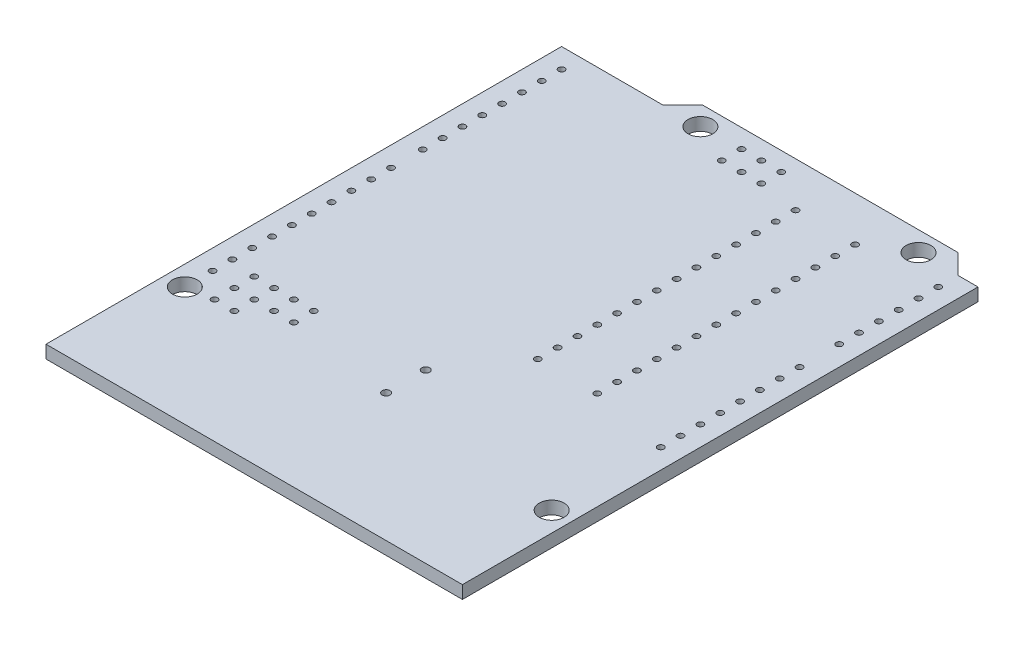
SolidWorks part; units mm, degrees
material "E-Glass Fiber"
ref_plane "Front Plane" through (0, 0, 0) normal (0, 0, 1) x (1, 0, 0)
ref_plane "Top Plane" through (0, 0, 0) normal (0, 1, 0) x (1, 0, 0)
ref_plane "Right Plane" through (0, 0, 0) normal (1, 0, 0) x (0, 0, -1)
sketch "Sketch1" plane through (0, 0, 0) normal (0, 1, 0) x (1, 0, 0)
  line L0 (-29.337, 0) -> (29.337, 0) construction
  line L1 (0, 0) -> (-53.34, 0)
  line L2 (0, 0) -> (0, 66.04)
  line L3 (-5.08, 68.58) -> (-37.846, 68.58)
  line L4 (-53.34, 0) -> (-53.34, 66.04)
  line L5 (-53.34, 66.04) -> (-40.386, 66.04)
  line L6 (-40.386, 66.04) -> (-37.846, 68.58)
  line L7 (-5.08, 68.58) -> (-2.54, 66.04)
  line L8 (-2.54, 66.04) -> (0, 66.04)
  circle A0 centre (-7.62, 66.04) radius 1.5875
  circle A1 centre (-35.56, 66.04) radius 1.5875
  circle A2 centre (-2.54, 13.97) radius 1.5875
  circle A3 centre (-50.8, 15.24) radius 1.5875
  dimension "D8" = 3.175
  dimension "D1" = 68.58
  dimension "D2" = 53.34
  dimension "D3" = 66.04
  dimension "D4" = 2.54
  dimension "D5" = 45
  dimension "D6" = 45
  dimension "D7" = 40.386
  dimension "D9" = 66.04
  dimension "D10" = 35.56
  dimension "D11" = 7.62
  dimension "D12" = 13.97
  dimension "D13" = 2.54
  dimension "D14" = 15.24
  dimension "D15" = 50.8
extrude "Boss-Extrude1" add sketch "Sketch1" against normal blind 1.65
sketch "Sketch2" plane through (0, 0, 0) normal (0, 1, 0) x (1, 0, 0)
  line L0 (0, -0.9075) -> (0, 0.9075) construction
  line L1 (-0.9075, 0) -> (0.9075, 0) construction
  circle A0 centre (-2.54, 27.94) radius 0.4
  dimension "D1" = 0.8
  dimension "D2" = 2.54
  dimension "D3" = 27.94
extrude "Cut-Extrude1" cut sketch "Sketch2" against normal blind 1.65
sketch "Sketch3" plane through (0, 0, 0) normal (0, 1, 0) x (1, 0, 0)
  line L0 (0, -0.9075) -> (0, 0.9075) construction
  line L1 (-0.9075, 0) -> (0.9075, 0) construction
  circle A0 centre (-50.8, 18.796) radius 0.4
  dimension "D2" = 0.8
  dimension "D1" = 50.8
  dimension "D3" = 18.796
extrude "Cut-Extrude2" cut sketch "Sketch3" against normal blind 1.65
pattern_linear "LPattern1" count 15 spacing 2.54 along (0, 0, -1) skipping (8, 0) of "Cut-Extrude1"
sketch "Sketch4" plane through (0, 0, 0) normal (0, 1, 0) x (1, 0, 0)
  line L0 (-0.9075, 0) -> (0.9075, 0) construction
  line L1 (0, -0.9075) -> (0, 0.9075) construction
  circle A0 centre (-50.8, 45.72) radius 0.4
  dimension "D3" = 0.8
  dimension "D1" = 45.72
  dimension "D2" = 50.8
extrude "Cut-Extrude3" cut sketch "Sketch4" against normal blind 1.65
pattern_linear "LPattern2" count 10 spacing 2.54 along (0, 0, -1) of "Cut-Extrude2"
pattern_linear "LPattern3" count 8 spacing 2.54 along (0, 0, -1) of "Cut-Extrude3"
sketch "Sketch5" plane through (0, 0, 0) normal (0, 1, 0) x (1, 0, 0)
  line L0 (-27.89, 66.18) -> (-27.89, 63.64) construction
  line L1 (-30.43, 66.18) -> (-25.35, 66.18) construction
  line L2 (-30.43, 66.18) -> (-30.43, 63.64) construction
  line L3 (-30.43, 63.64) -> (-25.35, 63.64) construction
  line L4 (-25.35, 66.18) -> (-25.35, 63.64) construction
  line L5 (-0.9075, 0) -> (0.9075, 0) construction
  line L6 (0, -0.9075) -> (0, 0.9075) construction
  circle A0 centre (-30.43, 66.18) radius 0.4
  circle A1 centre (-27.89, 66.18) radius 0.4
  circle A2 centre (-25.35, 66.18) radius 0.4
  circle A3 centre (-25.35, 63.64) radius 0.4
  circle A4 centre (-27.89, 63.64) radius 0.4
  circle A5 centre (-30.43, 63.64) radius 0.4
  circle A6 centre (-47.498, 15.748) radius 0.4
  circle A7 centre (-47.498, 18.288) radius 0.4
  circle A8 centre (-47.498, 20.828) radius 0.4
  circle A9 centre (-44.958, 20.828) radius 0.4
  circle A10 centre (-44.958, 18.288) radius 0.4
  circle A11 centre (-44.958, 15.748) radius 0.4
  circle A12 centre (-42.418, 18.288) radius 0.4
  circle A13 centre (-42.418, 20.828) radius 0.4
  circle A14 centre (-39.878, 20.828) radius 0.4
  circle A15 centre (-39.878, 18.288) radius 0.4
  circle A16 centre (-26.162, 21.463) radius 0.5
  circle A17 centre (-26.162, 16.383) radius 0.5
  dimension "D4" = 0.8
  dimension "D14" = 1
  dimension "D1" = 2.54
  dimension "D2" = 2.54
  dimension "D3" = 2.54
  dimension "D5" = 63.64
  dimension "D6" = 30.43
  dimension "D7" = 2.54
  dimension "D8" = 2.54
  dimension "D9" = 2.54
  dimension "D10" = 2.54
  dimension "D11" = 2.54
  dimension "D12" = 47.498
  dimension "D13" = 15.748
  dimension "D15" = 5.08
  dimension "D16" = 16.383
  dimension "D17" = 26.162
extrude "Cut-Extrude4" cut sketch "Sketch5" against normal blind 10
sketch "Sketch6" plane through (0, 0, 0) normal (0, 1, 0) x (1, 0, 0)
  line L0 (0, -37.719) -> (0, 37.719) construction
  line L1 (-29.337, 0) -> (29.337, 0) construction
  line L2 (-20.193, 29.845) -> (-20.193, 32.385) construction
  circle A0 centre (-20.193, 29.845) radius 0.4
  circle A1 centre (-12.573, 29.845) radius 0.4
  circle A2 centre (-20.193, 32.385) radius 0.4
  circle A3 centre (-12.573, 32.385) radius 0.4
  circle A4 centre (-20.193, 34.925) radius 0.4
  circle A5 centre (-12.573, 34.925) radius 0.4
  circle A6 centre (-20.193, 37.465) radius 0.4
  circle A7 centre (-12.573, 37.465) radius 0.4
  circle A8 centre (-20.193, 40.005) radius 0.4
  circle A9 centre (-12.573, 40.005) radius 0.4
  circle A10 centre (-20.193, 42.545) radius 0.4
  circle A11 centre (-12.573, 42.545) radius 0.4
  circle A12 centre (-20.193, 45.085) radius 0.4
  circle A13 centre (-12.573, 45.085) radius 0.4
  circle A14 centre (-20.193, 47.625) radius 0.4
  circle A15 centre (-12.573, 47.625) radius 0.4
  circle A16 centre (-20.193, 50.165) radius 0.4
  circle A17 centre (-12.573, 50.165) radius 0.4
  circle A18 centre (-20.193, 52.705) radius 0.4
  circle A19 centre (-12.573, 52.705) radius 0.4
  circle A20 centre (-20.193, 55.245) radius 0.4
  circle A21 centre (-12.573, 55.245) radius 0.4
  circle A22 centre (-20.193, 57.785) radius 0.4
  circle A23 centre (-12.573, 57.785) radius 0.4
  circle A24 centre (-20.193, 60.325) radius 0.4
  circle A25 centre (-12.573, 60.325) radius 0.4
  circle A26 centre (-20.193, 62.865) radius 0.4
  circle A27 centre (-12.573, 62.865) radius 0.4
  dimension "D1" = 0.8
  dimension "D2" = 7.62
  dimension "D3" = 12.573
  dimension "D4" = 29.845
  dimension "D6" = 2.54
  dimension "D5" = 14
extrude "Cut-Extrude5" cut sketch "Sketch6" against normal blind 10
move or copy body "Body-Move/Copy1" bodies to move or copy 110 copy no translate (50, 0, 0)
move or copy body "Body-Move/Copy2" bodies to move or copy 111 copy no translate (20, -240, 0)
move or copy body "Body-Move/Copy6" bodies to move or copy 112 copy no rotation origin (43.33, 0, -34.29) rotation axis (0, 1, 0) rotation angle 180
move or copy body "Body-Move/Copy7" bodies to move or copy 116 copy no rotation origin (43.33, 0, -34.29) rotation axis (0, 1, 0) rotation angle 180
move or copy body "Body-Move/Copy8" bodies to move or copy 117 copy no rotation origin (43.33, 0, -34.29) rotation axis (0, 1, 0) rotation angle 180
move or copy body "Body-Move/Copy9" bodies to move or copy 118 copy no rotation origin (43.33, 0, -34.29) rotation axis (0, 1, 0) rotation angle 180
equation "\"D13@Sketch5\"=0.001*25.4*620"
equation "\"D16@Sketch5\"=645*0.001*25.4"
